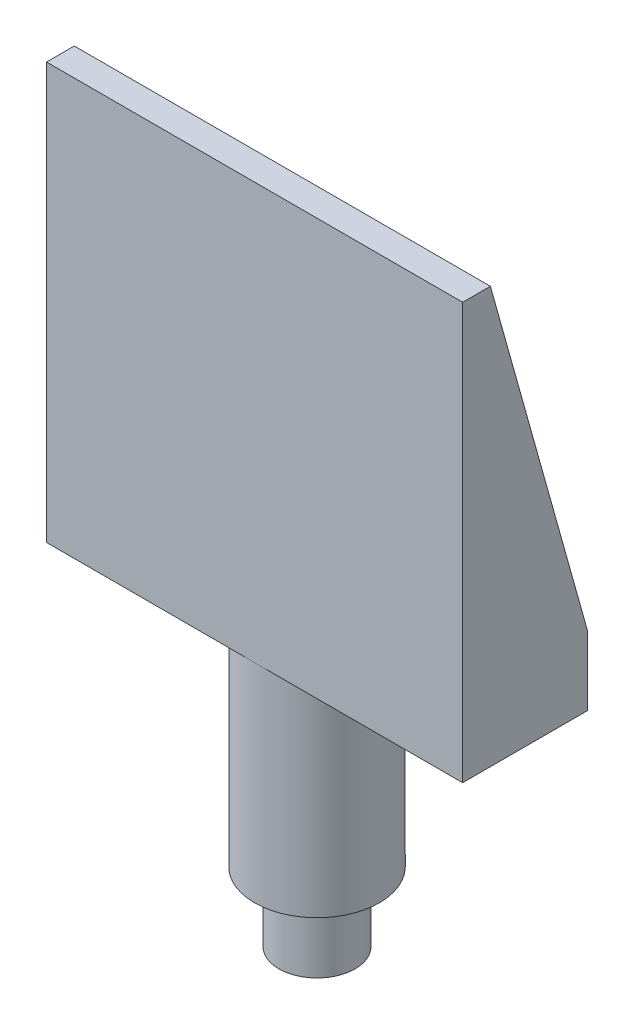
SolidWorks part; units mm, degrees
ref_plane "前视基准面" through (0, 0, 0) normal (0, 0, 1) x (1, 0, 0)
ref_plane "上视基准面" through (0, 0, 0) normal (0, 1, 0) x (1, 0, 0)
ref_plane "右视基准面" through (0, 0, 0) normal (1, 0, 0) x (0, 0, -1)
other "Configuration Table"
sketch "Sketch1" plane through (0, 0, 0) normal (0, 1, 0) x (1, 0, 0)
  circle A0 centre (0, 0) radius 2.75
  dimension "D1" = 5.5
extrude "Boss-Extrude1" add sketch "Sketch1" along normal blind 5
sketch "Sketch2" plane through (0, 5, 0) normal (0, 1, 0) x (1, 0, 0)
  circle A0 centre (0, 0) radius 4.5
  dimension "D1" = 9
extrude "Boss-Extrude2" add sketch "Sketch2" along normal blind 15
sketch "Sketch3" plane through (0, 20, 0) normal (0, 1, 0) x (1, 0, 0)
  line L1 (15, -4.5) -> (-15, -4.5)
  line L2 (15, -4.5) -> (15, 4.5)
  line L3 (15, 4.5) -> (-15, 4.5)
  line L4 (-15, -4.5) -> (-15, 4.5)
  line L5 (15, -4.5) -> (-15, 4.5) construction
  line L6 (15, 4.5) -> (-15, -4.5) construction
  point P0 (0, 0)
  dimension "D1" = 9
  dimension "D2" = 30
extrude "Boss-Extrude3" add sketch "Sketch3" along normal blind 30
sketch "Sketch4" plane through (0, 50, 0) normal (0, 1, 0) x (1, 0, 0)
  line L0 (15, 4.5) -> (-15, 4.5) construction
  line L1 (-13, 4.5) -> (13, 4.5)
  line L2 (-13, 4.5) -> (-13, -2.5)
  line L3 (-13, -2.5) -> (13, -2.5)
  line L4 (13, 4.5) -> (13, -2.5)
  line L5 (-15, 4.5) -> (-15, -4.5) construction
  line L6 (15, -4.5) -> (15, 4.5) construction
  line L7 (-15, -4.5) -> (15, -4.5) construction
  dimension "D1" = 2
  dimension "D2" = 2
  dimension "D3" = 2
extrude "Cut-Extrude1" cut sketch "Sketch4" against normal blind 25
sketch "Sketch5" plane through (15, 0, 0) normal (1, 0, 0) x (0, 0, -1)
  line L0 (-2.5, 50) -> (4.5, 25)
  line L1 (-4.5, 50) -> (4.5, 50) construction
  line L2 (4.5, 50) -> (4.5, 20) construction
  line L3 (-4.5, 50) -> (-4.5, 20) construction
  line L4 (4.5, 50) -> (-2.5, 50)
  line L5 (4.5, 50) -> (4.5, 25)
  dimension "D1" = 5
  dimension "D2" = 2
extrude "Cut-Extrude2" cut sketch "Sketch5" against normal blind 39
